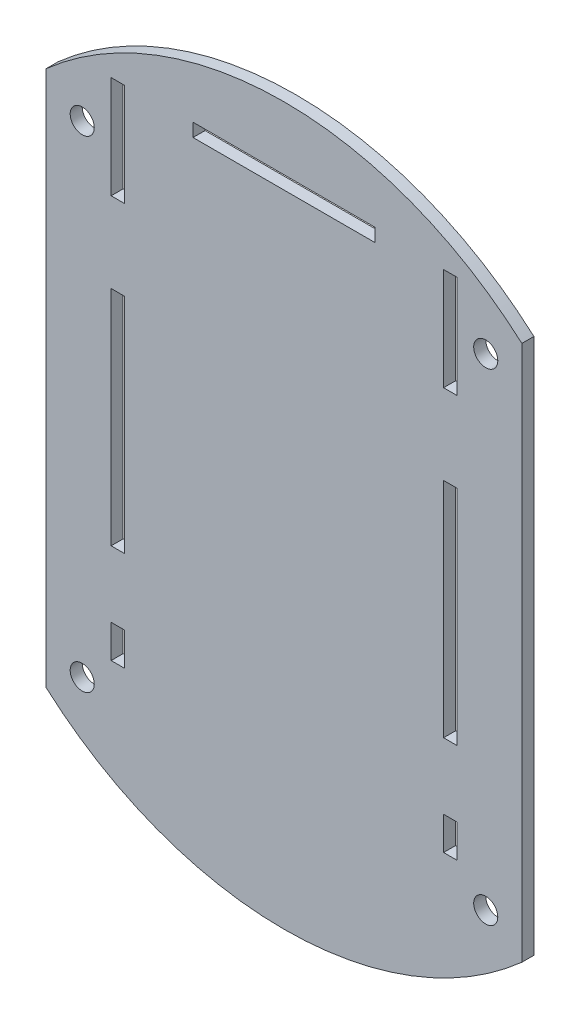
SolidWorks part; units mm, degrees
ref_plane "Ebene vorne" through (0, 0, 0) normal (0, 0, 1) x (1, 0, 0)
ref_plane "Ebene oben" through (0, 0, 0) normal (0, 1, 0) x (1, 0, 0)
ref_plane "Ebene rechts" through (0, 0, 0) normal (1, 0, 0) x (0, 0, -1)
sketch "Skizze1" plane through (0, 0, 0) normal (0, 0, 1) x (1, 0, 0)
  circle A0 centre (0, 0) radius 59.5
  dimension "D1" = 119
extrude "Aufsatz-Linear austragen1" add sketch "Skizze1" along normal blind 2
sketch "Skizze3" plane through (0, 0, 2) normal (0, 0, 1) x (1, 0, 0)
  line L0 (-26.5, 18.2886) -> (26.5, -18.7114) construction
  line L1 (-28.7, 18.2886) -> (-26.5, 18.2886)
  line L2 (-28.7, 18.2886) -> (-28.7, -18.7114)
  line L3 (-28.7, -18.7114) -> (-26.5, -18.7114)
  line L4 (-26.5, 18.2886) -> (-26.5, -18.7114)
  line L5 (26.5, 18.2886) -> (28.7, 18.2886)
  line L6 (26.5, 18.2886) -> (26.5, -18.7114)
  line L7 (26.5, -18.7114) -> (28.7, -18.7114)
  line L8 (28.7, 18.2886) -> (28.7, -18.7114)
  line L9 (-26.5, -18.7114) -> (26.5, 18.2886) construction
  line L10 (-28.7, 48.6206) -> (-28.7, 52.1206) construction
  line L11 (-28.7, 48.6206) -> (-26.5, 48.6206)
  line L12 (-28.7, 48.6206) -> (-28.7, 31.6206)
  line L13 (-28.7, 31.6206) -> (-26.5, 31.6206)
  line L14 (-26.5, 48.6206) -> (-26.5, 31.6206)
  line L15 (26.5, 48.6206) -> (28.7, 48.6206)
  line L16 (26.5, 48.6206) -> (26.5, 31.6206)
  line L17 (26.5, 31.6206) -> (28.7, 31.6206)
  line L18 (28.7, 48.6206) -> (28.7, 31.6206)
  line L19 (-28.7, -29.7114) -> (-26.5, -29.7114)
  line L20 (-28.7, -29.7114) -> (-28.7, -35.2114)
  line L21 (-28.7, -35.2114) -> (-26.5, -35.2114)
  line L22 (-26.5, -29.7114) -> (-26.5, -35.2114)
  line L23 (26.5, -29.7114) -> (28.7, -29.7114)
  line L24 (26.5, -29.7114) -> (26.5, -35.2114)
  line L25 (26.5, -35.2114) -> (28.7, -35.2114)
  line L26 (28.7, -29.7114) -> (28.7, -35.2114)
  line L31 (0, 0) -> (0, 59.5) construction
  line L34 (-33.5, 40) -> (-33.5, -40) construction
  line L35 (-33.5, -40) -> (33.5, -40) construction
  line L36 (33.5, 40) -> (33.5, -40) construction
  line L37 (-33.5, 40) -> (0, 40) construction
  line L38 (0, 40) -> (33.5, 40) construction
  line L39 (-33.5, 40) -> (33.5, -40) construction
  line L40 (-33.5, -40) -> (33.5, 40) construction
  line L41 (27.6, -35.2114) -> (27.6, -52.7114) construction
  line L44 (15.1, 49) -> (-15.1, 49)
  line L45 (15.1, 49) -> (15.1, 46.8)
  line L46 (15.1, 46.8) -> (-15.1, 46.8)
  line L47 (-15.1, 49) -> (-15.1, 46.8)
  line L48 (-15.1, 47.9) -> (-26.5, 47.9) construction
  line L49 (15.1, 47.9) -> (26.5, 47.9) construction
  line L50 (39.5, -0.2114) -> (28.7, -0.2114) construction
  line L51 (39.5, -44.4972) -> (59.5, -44.4972)
  line L52 (39.5, -44.4972) -> (39.5, 44.4972)
  line L53 (39.5, 44.4972) -> (59.5, 44.4972)
  line L54 (59.5, -44.4972) -> (59.5, 44.4972)
  line L55 (-39.5, 44.4972) -> (-59.5, 44.4972)
  line L56 (-39.5, 44.4972) -> (-39.5, -44.4972)
  line L57 (-39.5, -44.4972) -> (-59.5, -44.4972)
  line L58 (-59.5, 44.4972) -> (-59.5, -44.4972)
  line L59 (-39.5, -5.1281) -> (-28.7, -5.1281) construction
  line L60 (0, 49) -> (0, 59.5) construction
  circle A0 centre (-33.5, 40) radius 2
  circle A1 centre (0, 0) radius 59.5 construction
  circle A6 centre (33.5, 40) radius 2
  circle A7 centre (33.5, -40) radius 2
  circle A8 centre (-33.5, -40) radius 2
  point P37 (0, -0.2114)
  point P38 (0, -0.2114)
  point P39 (0, -40)
  point P43 (0, 0)
  dimension "D14" = 4
  dimension "D15" = 4
  dimension "D16" = 4
  dimension "D17" = 4
  dimension "D1" = 2.2
  dimension "D2" = 2.2
  dimension "D3" = 53
  dimension "D4" = 17
  dimension "D5" = 37
  dimension "D6" = 5.5
  dimension "D7" = 17.5
  dimension "D8" = 11
  dimension "D9" = 30.2
  dimension "D10" = 2.2
  dimension "D11" = 3.5
  dimension "D12" = 67
  dimension "D13" = 80
  dimension "D18" = 20
  dimension "D19" = 10.5
extrude "Schnitt-Linear austragen7" cut sketch "Skizze3" against normal up to surface (2 mm away) up to face at (59.5, 0, 0)
